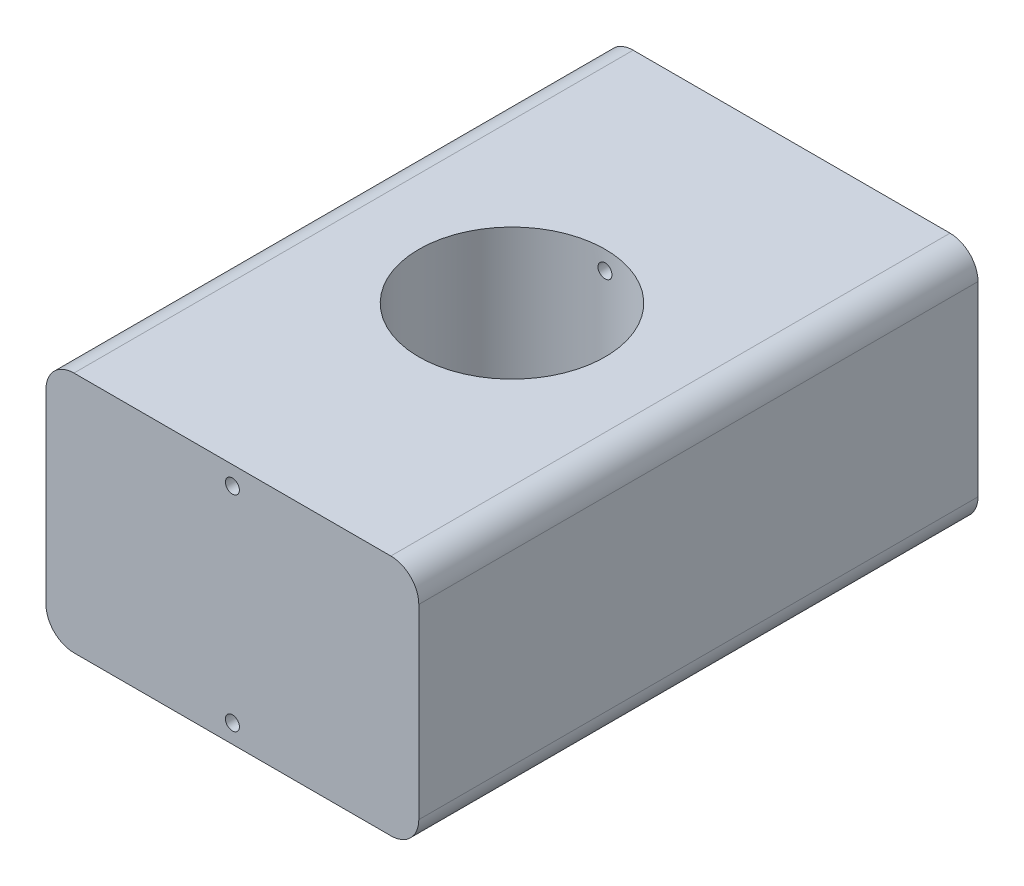
SolidWorks part; units mm, degrees
ref_plane "Front Plane" through (0, 0, 0) normal (0, 0, 1) x (1, 0, 0)
ref_plane "Top Plane" through (0, 0, 0) normal (0, 1, 0) x (1, 0, 0)
ref_plane "Right Plane" through (0, 0, 0) normal (1, 0, 0) x (0, 0, -1)
sketch "Sketch1" plane through (0, 0, 0) normal (0, 0, 1) x (1, 0, 0)
  line L0 (0, -13) -> (0, 13) construction
  line L1 (-20, -13) -> (20, -13)
  line L2 (-20, -13) -> (-20, 13)
  line L3 (-20, 13) -> (20, 13)
  line L4 (20, -13) -> (20, 13)
  line L5 (-20, -13) -> (20, 13) construction
  line L6 (-20, 13) -> (20, -13) construction
  circle A0 centre (0, 11) radius 0.75
  circle A1 centre (0, -11) radius 0.75
  point P0 (0, 0)
  point P9 (0, 0)
  dimension "D4" = 1.5
  dimension "D6" = 1.5
  dimension "D1" = 40
  dimension "D2" = 26
  dimension "D3" = 2
  dimension "D5" = 2
extrude "Boss-Extrude1" add sketch "Sketch1" along normal blind 60
fillet "Fillet1" radius 3 1 edges at (20, 13, 30)
fillet "Fillet2" radius 3 3 edges at (-20, -13, 30) (-20, 13, 30) (20, -13, 30)
sketch "Sketch2" plane through (0, 13, 0) normal (0, 1, 0) x (1, 0, 0)
  line L0 (0, 0) -> (0, -60) construction
  line L1 (17, -60) -> (-17, -60) construction
  circle A0 centre (0, -30) radius 10
  dimension "D1" = 20
extrude "Cut-Extrude1" cut sketch "Sketch2" against normal through all contours A0
